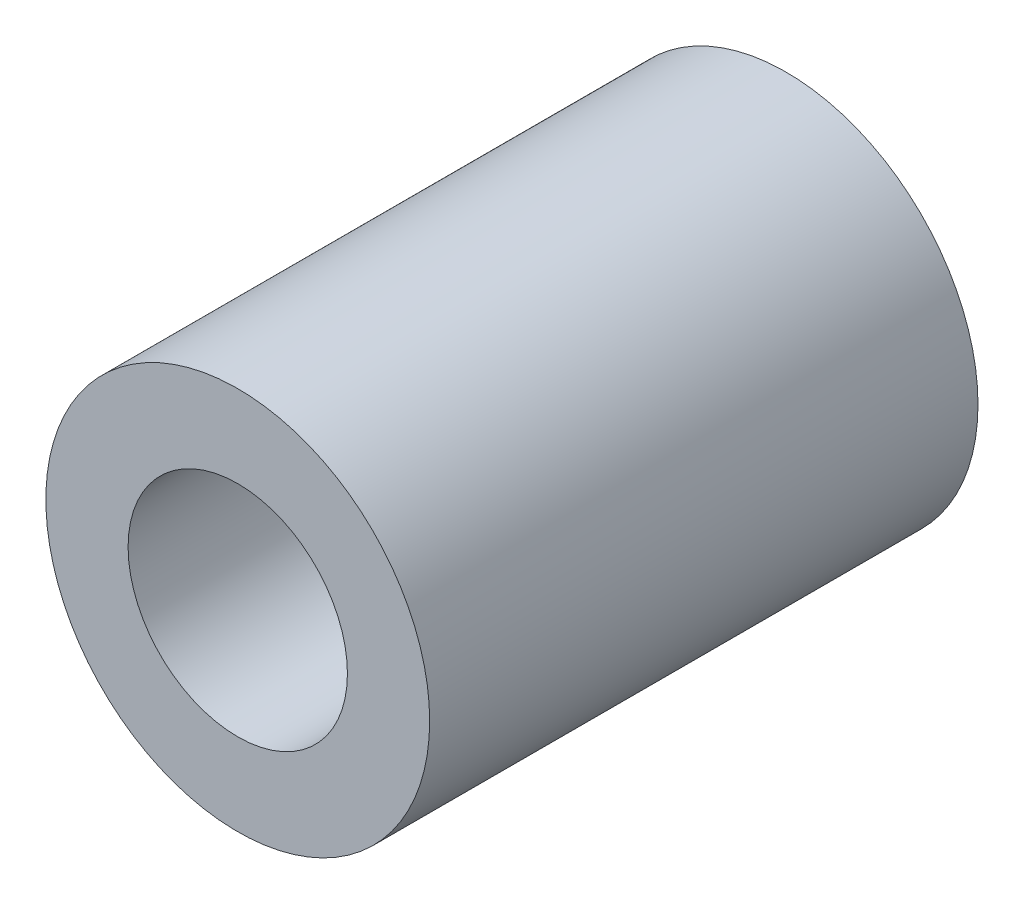
SolidWorks part; units mm, degrees
ref_plane "Front Plane" through (0, 0, 0) normal (0, 0, 1) x (1, 0, 0)
ref_plane "Top Plane" through (0, 0, 0) normal (0, 1, 0) x (1, 0, 0)
ref_plane "Right Plane" through (0, 0, 0) normal (1, 0, 0) x (0, 0, -1)
sketch "Sketch1" plane through (0, 0, 0) normal (0, 0, 1) x (1, 0, 0)
  circle A0 centre (0, 0) radius 10.5
  circle A1 centre (0, 0) radius 6
  dimension "D1" = 21
extrude "Boss-Extrude1" add sketch "Sketch1" along normal blind 30
